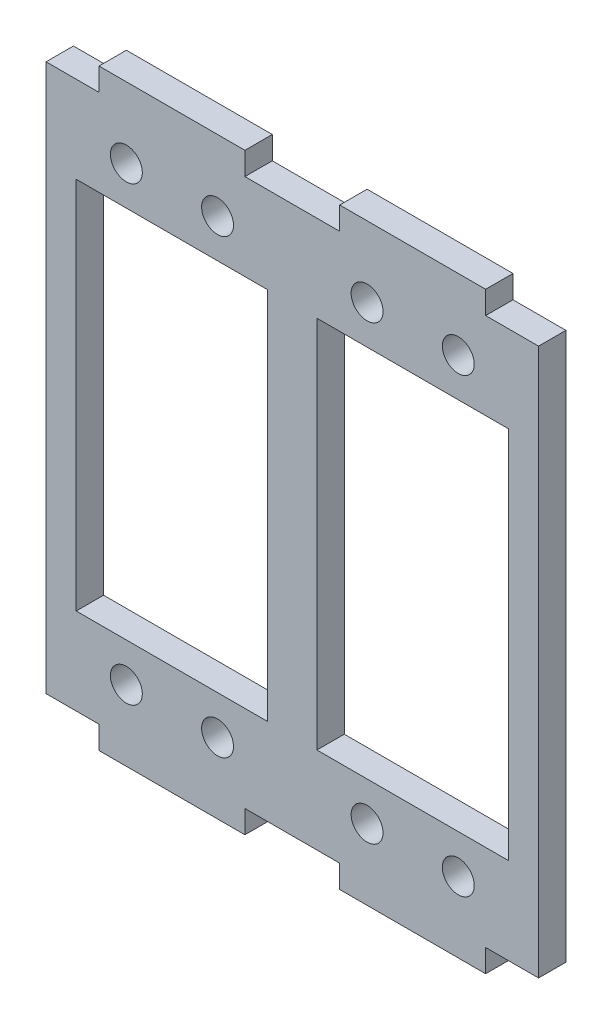
SolidWorks part; units mm, degrees
material "PMMA"
ref_plane "Спереди" through (0, 0, 0) normal (0, 0, 1) x (1, 0, 0)
ref_plane "Сверху" through (0, 0, 0) normal (0, 1, 0) x (1, 0, 0)
ref_plane "Справа" through (0, 0, 0) normal (1, 0, 0) x (0, 0, -1)
sketch "Эскиз1" plane through (0, 0, 0) normal (0, 0, 1) x (1, 0, 0)
  line L0 (0, 0) -> (0, 15.5674) construction
  line L1 (0, 0) -> (-28.7108, 0) construction
  line L2 (-13.1973, 26.8793) -> (-13.1973, -23.6473) construction
  line L3 (13.1973, -7.7029) -> (13.1973, 19.6612) construction
  line L4 (-55.8594, -10.1) -> (29.6804, -10.1) construction
  line L5 (-21.1973, 19.9) -> (-21.1973, 22.4)
  line L6 (-2.6973, -30.6) -> (-23.6973, -30.6)
  line L7 (-2.6973, -30.6) -> (-2.6973, 10.4)
  line L8 (-2.6973, 10.4) -> (-23.6973, 10.4)
  line L9 (-23.6973, -30.6) -> (-23.6973, 10.4)
  line L10 (-2.6973, -30.6) -> (-23.6973, 10.4) construction
  line L11 (-2.6973, 10.4) -> (-23.6973, -30.6) construction
  line L12 (23.6973, -30.6) -> (2.6973, -30.6)
  line L13 (23.6973, -30.6) -> (23.6973, 10.4)
  line L14 (23.6973, 10.4) -> (2.6973, 10.4)
  line L15 (2.6973, -30.6) -> (2.6973, 10.4)
  line L16 (23.6973, -30.6) -> (2.6973, 10.4) construction
  line L17 (23.6973, 10.4) -> (2.6973, -30.6) construction
  line L18 (-8.1973, -34.85) -> (-18.1973, -34.85) construction
  line L19 (-8.1973, -34.85) -> (-8.1973, 14.65) construction
  line L20 (-8.1973, 14.65) -> (-18.1973, 14.65) construction
  line L21 (-18.1973, -34.85) -> (-18.1973, 14.65) construction
  line L22 (-8.1973, -34.85) -> (-18.1973, 14.65) construction
  line L23 (-8.1973, 14.65) -> (-18.1973, -34.85) construction
  line L24 (18.1973, -34.85) -> (8.1973, -34.85) construction
  line L25 (18.1973, -34.85) -> (18.1973, 14.65) construction
  line L26 (18.1973, 14.65) -> (8.1973, 14.65) construction
  line L27 (8.1973, -34.85) -> (8.1973, 14.65) construction
  line L28 (18.1973, -34.85) -> (8.1973, 14.65) construction
  line L29 (18.1973, 14.65) -> (8.1973, -34.85) construction
  line L30 (27, -40.1) -> (-27, -40.1)
  line L31 (27, -40.1) -> (27, 19.9)
  line L32 (27, 19.9) -> (-27, 19.9)
  line L33 (-27, -40.1) -> (-27, 19.9)
  line L34 (27, -40.1) -> (-27, 19.9) construction
  line L35 (27, 19.9) -> (-27, -40.1) construction
  line L36 (-21.1973, 22.4) -> (-5.1973, 22.4)
  line L37 (-5.1973, 22.4) -> (-5.1973, 19.9)
  line L38 (5.1973, 19.9) -> (5.1973, 22.4)
  line L39 (5.1973, 22.4) -> (21.1973, 22.4)
  line L40 (21.1973, 22.4) -> (21.1973, 19.9)
  line L41 (-21.1973, -40.1) -> (-21.1973, -42.6)
  line L42 (-21.1973, -42.6) -> (-5.1973, -42.6)
  line L43 (-5.1973, -42.6) -> (-5.1973, -40.1)
  line L44 (5.1973, -40.1) -> (5.1973, -42.6)
  line L45 (5.1973, -42.6) -> (21.1973, -42.6)
  line L46 (21.1973, -42.6) -> (21.1973, -40.1)
  circle A0 centre (-18.1973, -34.85) radius 1.75
  circle A1 centre (-8.1973, -34.85) radius 1.75
  circle A2 centre (8.1973, -34.85) radius 1.75
  circle A3 centre (18.1973, -34.85) radius 1.75
  circle A4 centre (18.1973, 14.65) radius 1.75
  circle A5 centre (8.1973, 14.65) radius 1.75
  circle A6 centre (-8.1973, 14.65) radius 1.75
  circle A7 centre (-18.1973, 14.65) radius 1.75
  point P11 (-13.1973, -10.1)
  point P13 (13.1973, -10.1)
  point P14 (-13.1973, -10.1)
  point P19 (13.1973, -10.1)
  point P24 (-13.1973, -10.1)
  point P29 (13.1973, -10.1)
  point P34 (0, -10.1)
  point P35 (0, -10.1)
  point P48 (-21.1973, 21.15)
  dimension "D26" = 30
  dimension "D1" = 13.1973
  dimension "D2" = 13.1973
  dimension "D3" = 10.1
  dimension "D4" = 21
  dimension "D5" = 41
  dimension "D6" = 41
  dimension "D7" = 21
  dimension "D8" = 10
  dimension "D9" = 10
  dimension "D10" = 49.5
  dimension "D11" = 49.5
  dimension "D12" = 60
  dimension "D13" = 54
  dimension "D14" = 2.5
  dimension "D15" = 2.5
  dimension "D16" = 8
  dimension "D17" = 16
  dimension "D18" = 16
  dimension "D19" = 8
  dimension "D20" = 8
  dimension "D21" = 16
  dimension "D22" = 8
  dimension "D23" = 16
  dimension "D24" = 2.5
  dimension "D25" = 2.5
extrude "Бобышка-Вытянуть1" add sketch "Эскиз1" against normal blind 3 contours L33 L30 L31 L32 A7 A6 A5 A4 A3 A2 A1 A0 L6 L9 L8 L7 L12 L15 L14 L13 | L37 L36 L5 L32 | L40 L39 L38 L32 | L45 L46 L30 L44 | L42 L43 L30 L41
